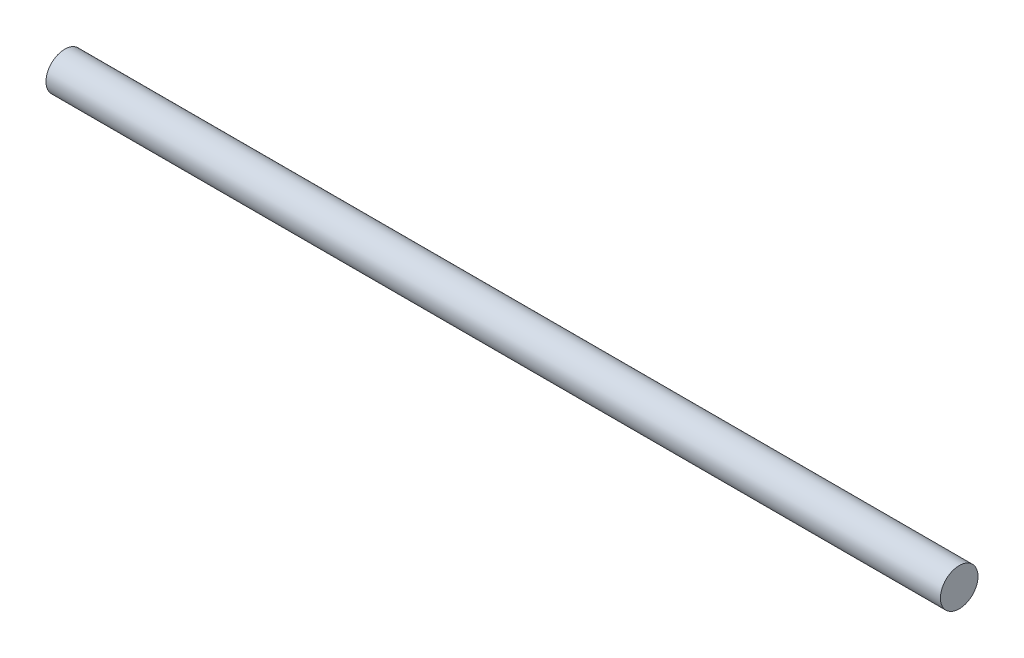
SolidWorks part; units mm, degrees
ref_plane "Front Plane" through (0, 0, 0) normal (0, 0, 1) x (1, 0, 0)
ref_plane "Top Plane" through (0, 0, 0) normal (0, 1, 0) x (1, 0, 0)
ref_plane "Right Plane" through (0, 0, 0) normal (1, 0, 0) x (0, 0, -1)
sketch "Sketch1" plane through (0, 0, 0) normal (1, 0, 0) x (0, 0, -1)
  circle A0 centre (0, 0) radius 6.25
  dimension "D1" = 12.5
extrude "Boss-Extrude1" add sketch "Sketch1" along normal mid plane 297.5
